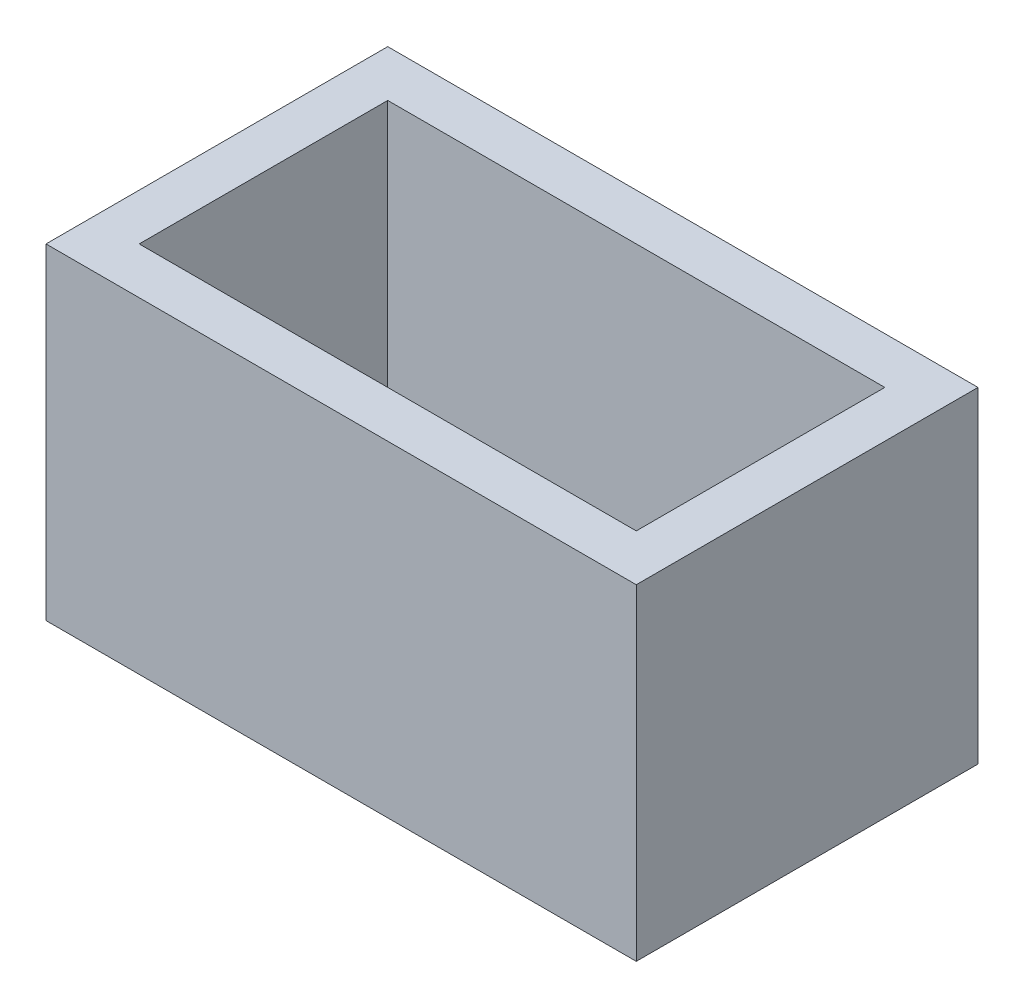
SolidWorks part; units mm, degrees
ref_plane "Front Plane" through (0, 0, 0) normal (0, 0, 1) x (1, 0, 0)
ref_plane "Top Plane" through (0, 0, 0) normal (0, 1, 0) x (1, 0, 0)
ref_plane "Right Plane" through (0, 0, 0) normal (1, 0, 0) x (0, 0, -1)
sketch "Sketch1" plane through (0, 0, 0) normal (0, 1, 0) x (1, 0, 0)
  line L1 (0, 0) -> (20, 0)
  line L2 (0, 0) -> (0, 12)
  line L3 (0, 12) -> (20, 12)
  line L4 (20, 0) -> (20, 12)
  dimension "D1" = 12
  dimension "D2" = 20
extrude "Boss-Extrude1" add sketch "Sketch1" along normal blind 11
shell "Shell1" thickness 2
sketch "Sketch2" plane through (0, 2, 0) normal (0, 1, 0) x (1, 0, 0)
  line L0 (20, 0) -> (20, 12) construction
  line L1 (20, 12) -> (0, 12) construction
  circle A0 centre (6, 6) radius 3
  point P0 (6, 6)
  dimension "D3" = 6
  dimension "D1" = 14
  dimension "D2" = 6
sketch "Sketch3" plane through (0, 0, 0) normal (0, -1, 0) x (1, 0, 0)
  circle A0 centre (6, -4.73) radius 0.625
  circle A1 centre (6, -7.27) radius 0.625
  point P0 (6, -4.73)
  point P1 (6, -7.27)
  dimension "D1" = 1.25
  dimension "D2" = 1.25
extrude "Cut-Extrude1" cut sketch "Sketch3" against normal blind 10
pattern_linear "LPattern1" count 2 spacing 8 along (1, 0, 0) of "Cut-Extrude1"
sketch "Sketch5" plane through (0, 11, 0) normal (0, 1, 0) x (1, 0, 0)
  line L10 (20, 0) -> (20, 12) construction
  line L11 (0, 0) -> (20, 0) construction
  line L12 (0, 12) -> (0, 0) construction
  line L13 (20, 12) -> (0, 12) construction
  line L14 (19.5, 0.5) -> (19.5, 11.5)
  line L15 (0.5, 0.5) -> (19.5, 0.5)
  line L16 (0.5, 11.5) -> (0.5, 0.5)
  line L17 (19.5, 11.5) -> (0.5, 11.5)
  line L18 (19.5, 0.5) -> (19.5, 11.5)
  line L19 (0.5, 0.5) -> (19.5, 0.5)
  line L20 (0.5, 11.5) -> (0.5, 0.5)
  line L21 (19.5, 11.5) -> (0.5, 11.5)
  line L22 (20, 0) -> (20, 12)
  line L23 (0, 0) -> (20, 0)
  line L24 (0, 12) -> (0, 0)
  line L25 (20, 12) -> (0, 12)
  dimension "D1" = 0.5
extrude "Cut-Extrude2" cut sketch "Sketch5" against normal through all
sketch "Sketch6" plane through (0, 0, 0) normal (0, -1, 0) x (1, 0, 0)
  line L4 (19.5, -11.5) -> (19.5, -0.5)
  line L5 (19.5, -0.5) -> (0.5, -0.5)
  line L6 (0.5, -0.5) -> (0.5, -11.5)
  line L7 (0.5, -11.5) -> (19.5, -11.5)
  line L8 (19.5, -11.5) -> (19.5, -0.5)
  line L9 (19.5, -0.5) -> (0.5, -0.5)
  line L10 (0.5, -0.5) -> (0.5, -11.5)
  line L11 (0.5, -11.5) -> (19.5, -11.5)
  dimension "D1" = 0
extrude "Cut-Extrude3" cut sketch "Sketch6" against normal blind 0.5
